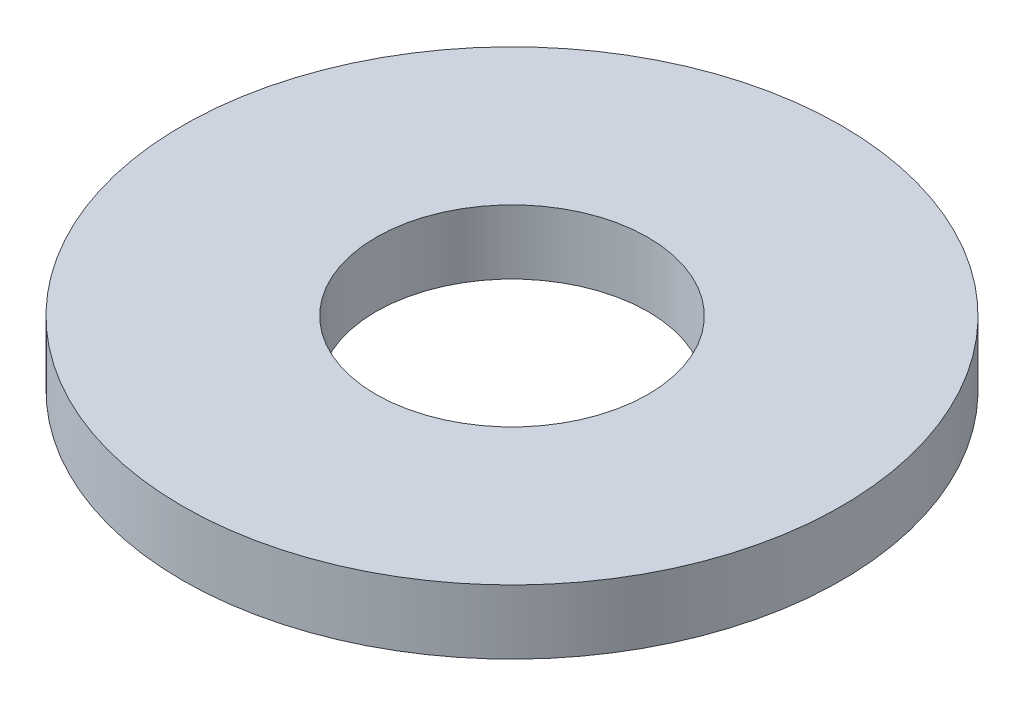
SolidWorks part; units mm, degrees
material "Alloy Steel"
ref_plane "Front Plane" through (0, 0, 0) normal (0, 0, 1) x (1, 0, 0)
ref_plane "Top Plane" through (0, 0, 0) normal (0, 1, 0) x (1, 0, 0)
ref_plane "Right Plane" through (0, 0, 0) normal (1, 0, 0) x (0, 0, -1)
sketch "Sketch1" plane through (0, 0, 0) normal (0, 1, 0) x (1, 0, 0)
  circle A0 centre (0, 0) radius 3.302
  circle A1 centre (0, 0) radius 8
  dimension "D1" = 16
  dimension "D2" = 6.604
extrude "Boss-Extrude1" add sketch "Sketch1" along normal blind 1.56
move or copy body "Body-Move/Copy1" bodies to move or copy 101
